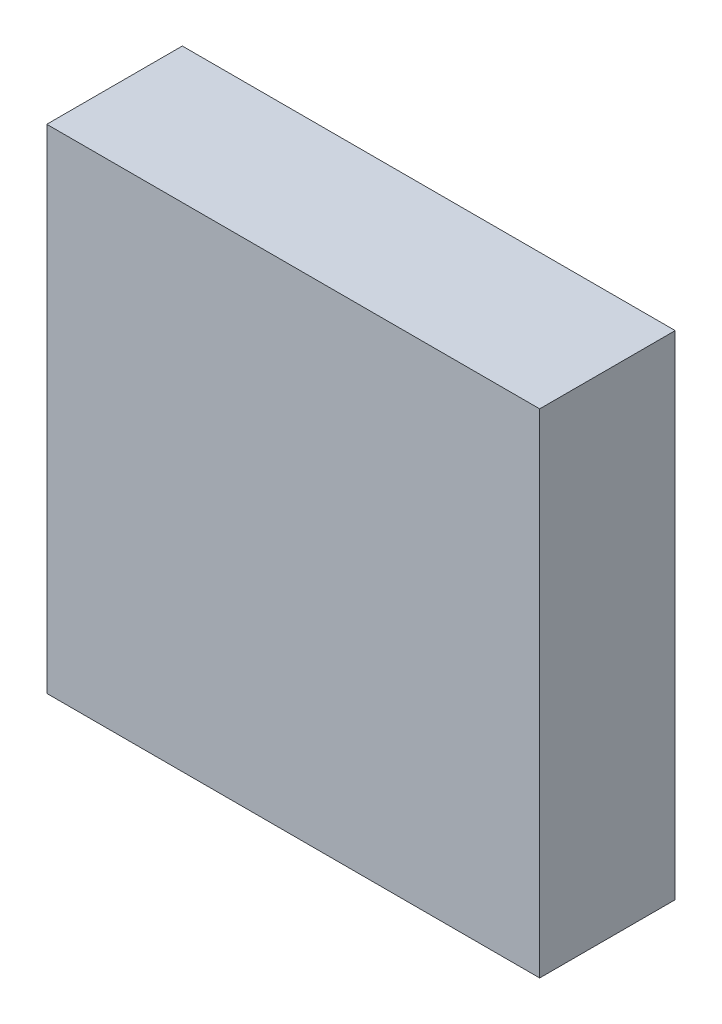
SolidWorks part; units mm, degrees
ref_plane "Спереди" through (0, 0, 0) normal (0, 0, 1) x (1, 0, 0)
ref_plane "Сверху" through (0, 0, 0) normal (0, 1, 0) x (1, 0, 0)
ref_plane "Справа" through (0, 0, 0) normal (1, 0, 0) x (0, 0, -1)
sketch "Эскиз1" plane through (0, 0, 0) normal (0, 0, 1) x (1, 0, 0)
  line L1 (0, 0) -> (4, 0)
  line L2 (0, 0) -> (0, 4)
  line L3 (0, 4) -> (4, 4)
  line L4 (4, 0) -> (4, 4)
extrude "Бобышка-Вытянуть1" add sketch "Эскиз1" along normal blind 1.1
